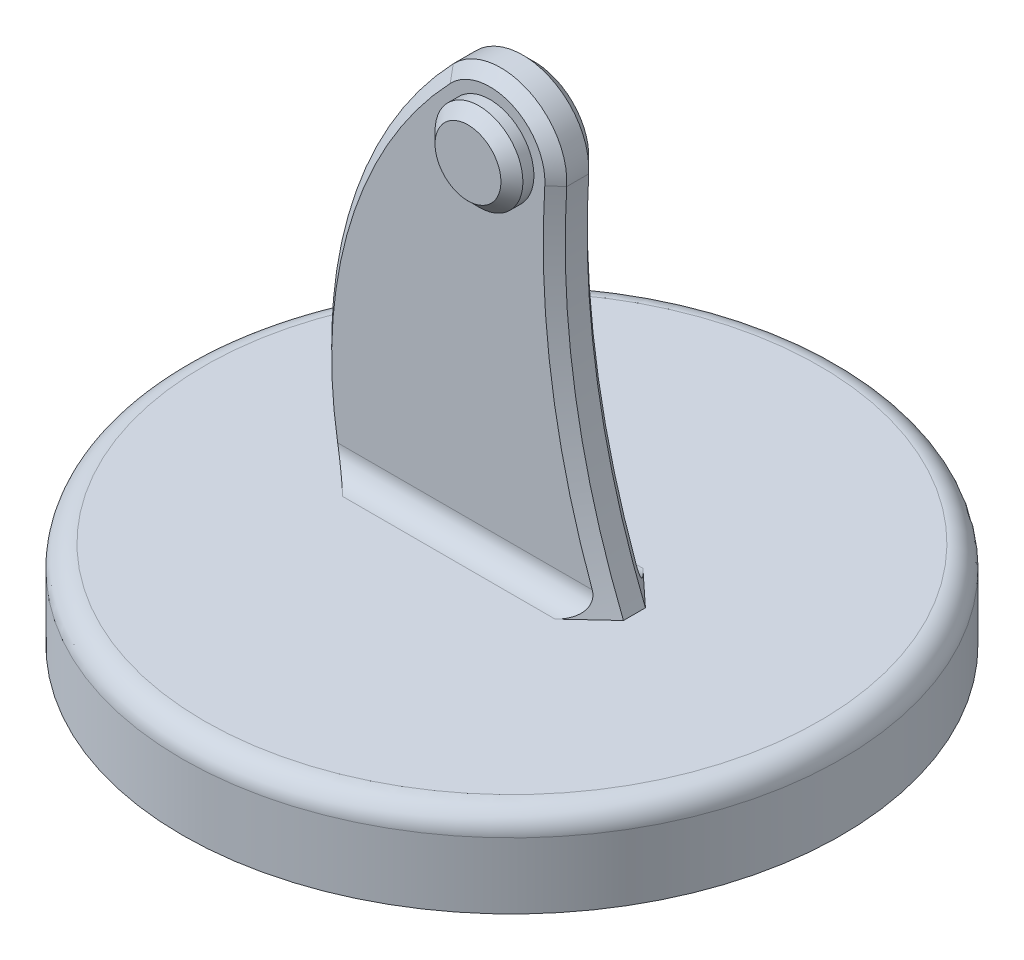
SolidWorks part; units mm, degrees
ref_plane "Alzado" through (0, 0, 0) normal (0, 0, 1) x (1, 0, 0)
ref_plane "Planta" through (0, 0, 0) normal (0, 1, 0) x (1, 0, 0)
ref_plane "Vista lateral" through (0, 0, 0) normal (1, 0, 0) x (0, 0, -1)
sketch "Sketch1" plane through (0, 0, 0) normal (0, 1, 0) x (1, 0, 0)
  circle A0 centre (0, 0) radius 75
  dimension "D1" = 150
extrude "Boss-Extrude1" add sketch "Sketch1" along normal blind 20
fillet "Fillet3" radius 5 1 edges at (0, 20, 75)
sketch "Sketch3" plane through (0, 0, 0) normal (0, 0, 1) x (1, 0, 0)
  line L0 (0, 0) -> (0, 100) construction
  line L1 (-75, 15) -> (75, 15) construction
  line L2 (-35, 15) -> (30, 15)
  arc A0 (14.9706, 99.062) -> (-10.8492, 110.3583) centre (0, 100) ccw
  arc A1 (-35, 15) -> (-10.8492, 110.3583) centre (61.4788, 41.3028) cw
  arc A2 (14.9706, 99.062) -> (30, 15) centre (194.6184, 87.8065) ccw
  point P13 (17.4281, 56.1268)
  point P14 (-35.4605, 65.8541)
  dimension "D4" = 30
  dimension "D1" = 30
  dimension "D2" = 35
  dimension "D3" = 100
  dimension "D5" = 180
  dimension "D6" = 100
extrude "Boss-Extrude2" add sketch "Sketch3" along normal mid plane 10
chamfer "Chamfer1" distance 2.5 angle 45 6 edges at (16.9703, 58.8038, -5) (-34.7965, 68.3412, -5) (6.0123, 113.7423, -5) (-34.7965, 68.3412, 5) (6.0123, 113.7423, 5) (16.9703, 58.8038, 5)
fillet "Fillet4" radius 5 2 edges at (-4.2415, 20, -5) (-4.2415, 20, 5)
sketch "Sketch4" plane through (0, 0, 5) normal (0, 0, 1) x (1, 0, 0)
  circle A0 centre (0, 100) radius 10
  dimension "D1" = 20
extrude "Boss-Extrude3" add sketch "Sketch4" along normal blind 5
chamfer "Chamfer2" distance 2.5 angle 45 1 edges at (10, 100, 10)
sketch "Sketch5" plane through (0, 0, -5) normal (0, 0, -1) x (-1, 0, 0)
  circle A0 centre (0, 100) radius 5
  dimension "D1" = 10
extrude "Cut-Extrude1" cut sketch "Sketch5" against normal blind 10 contours A0
